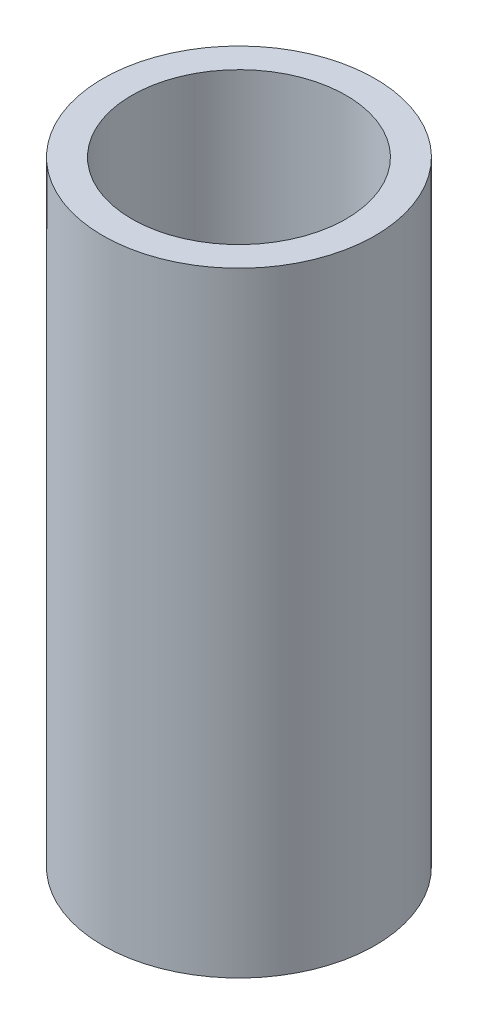
SolidWorks part; units mm, degrees
material "PBT Общее назначение"
ref_plane "Спереди" through (0, 0, 0) normal (0, 0, 1) x (1, 0, 0)
ref_plane "Сверху" through (0, 0, 0) normal (0, 1, 0) x (1, 0, 0)
ref_plane "Справа" through (0, 0, 0) normal (1, 0, 0) x (0, 0, -1)
sketch "Эскиз1" plane through (0, 0, 0) normal (0, 1, 0) x (1, 0, 0)
  circle A0 centre (0, 0) radius 12.2
  circle A1 centre (0, 0) radius 15.5
  dimension "D1" = 24.4
  dimension "D2" = 31
extrude "Бобышка-Вытянуть1" add sketch "Эскиз1" along normal blind 70
